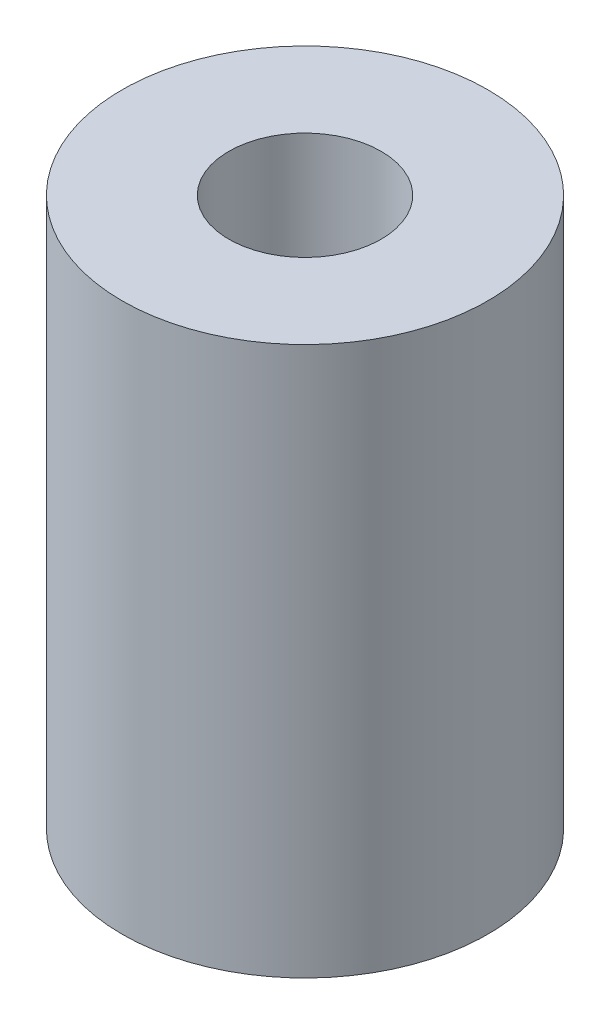
SolidWorks part; units mm, degrees
material "Rubber"
ref_plane "Front Plane" through (0, 0, 0) normal (0, 0, 1) x (1, 0, 0)
ref_plane "Top Plane" through (0, 0, 0) normal (0, 1, 0) x (1, 0, 0)
ref_plane "Right Plane" through (0, 0, 0) normal (1, 0, 0) x (0, 0, -1)
sketch "Sketch1" plane through (0, 0, 0) normal (0, 0, 1) x (1, 0, 0)
  line L0 (0, 0) -> (0, 21308.6818) construction
  line L1 (2.5, 0) -> (2.5, 18)
  line L2 (2.5, 18) -> (6, 18)
  line L3 (6, 18) -> (6, 0)
  line L4 (6, 0) -> (2.5, 0)
  point P5 (0, 0)
  dimension "D1" = 18
  dimension "D2" = 2.5
  dimension "D3" = 6
revolve "Revolve1" add sketch "Sketch1" angle 360 about L0
